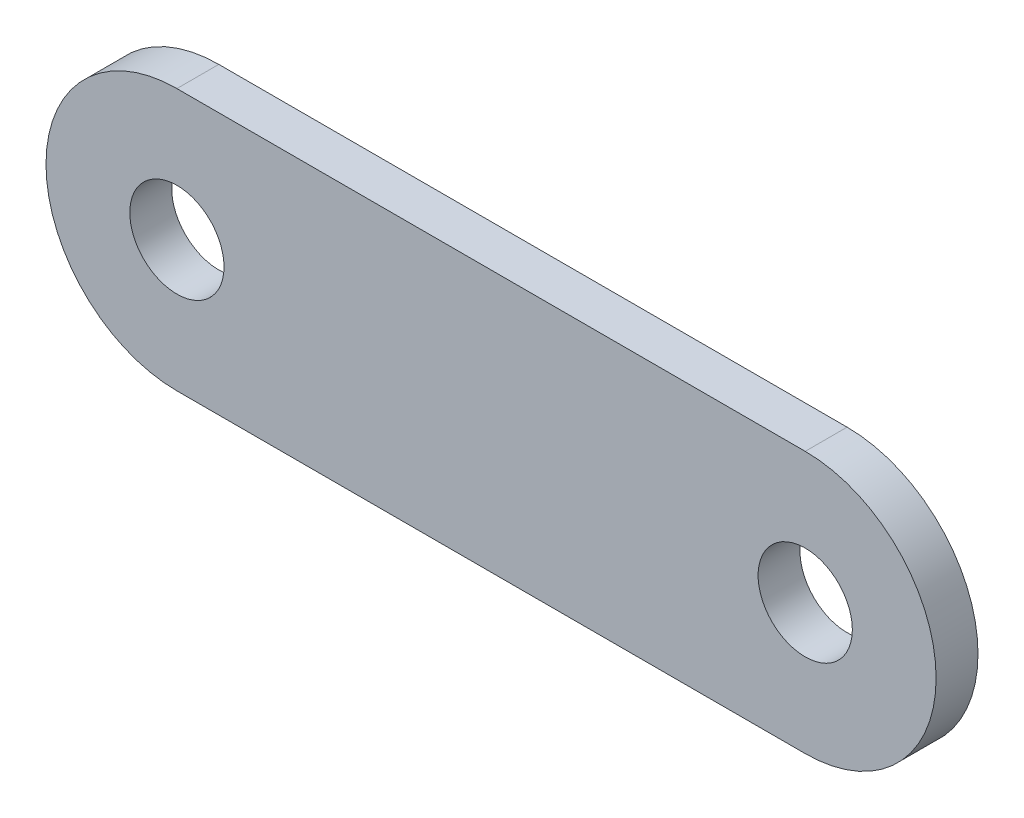
SolidWorks part; units mm, degrees
ref_plane "Ebene vorne" through (0, 0, 0) normal (0, 0, 1) x (1, 0, 0)
ref_plane "Ebene oben" through (0, 0, 0) normal (0, 1, 0) x (1, 0, 0)
ref_plane "Ebene rechts" through (0, 0, 0) normal (1, 0, 0) x (0, 0, -1)
sketch "Skizze1" plane through (0, 0, 0) normal (0, 0, 1) x (1, 0, 0)
  line L0 (0, 0) -> (60, 0) construction
  line L1 (0, 0) -> (60, 0) construction
  line L2 (0, 12.5) -> (60, 12.5)
  line L3 (0, -12.5) -> (60, -12.5)
  circle A0 centre (0, 0) radius 4.5
  circle A1 centre (60, 0) radius 4.5
  arc A2 (0, 12.5) -> (0, -12.5) centre (0, 0) ccw
  arc A3 (60, -12.5) -> (60, 12.5) centre (60, 0) ccw
  point P5 (30, 0)
  dimension "D1" = 9
  dimension "D2" = 60
  dimension "D3" = 25
extrude "Aufsatz-Linear austragen1" add sketch "Skizze1" along normal blind 4
